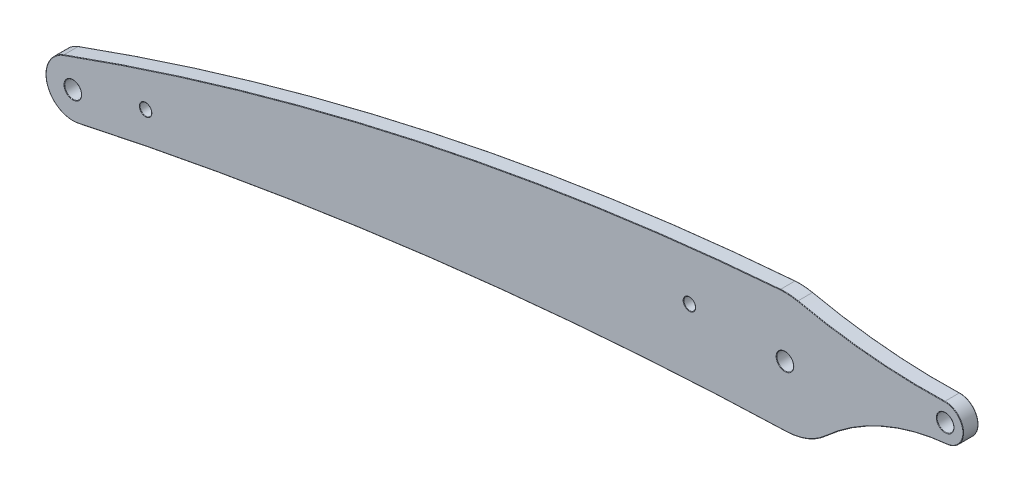
SolidWorks part; units mm, degrees
ref_plane "Front Plane" through (0, 0, 0) normal (0, 0, 1) x (1, 0, 0)
ref_plane "Top Plane" through (0, 0, 0) normal (0, 1, 0) x (1, 0, 0)
ref_plane "Right Plane" through (0, 0, 0) normal (1, 0, 0) x (0, 0, -1)
sketch "Sketch1" plane through (0, 0, 0) normal (0, 0, 1) x (1, 0, 0)
  line L0 (-273.7014, 238.8239) -> (16.1627, 287.9649) construction
  line L1 (-273.7014, 238.8239) -> (16.1627, 287.9649) construction
  circle A0 centre (-273.7014, 238.8239) radius 9 construction
  circle A1 centre (-37.0777, 278.939) radius 10 construction
  circle A2 centre (-37.0777, 278.939) radius 20 construction
  circle A3 centre (16.1627, 287.9649) radius 6 construction
  arc A4 (-276.7803, 247.2809) -> (-38.6275, 298.8789) centre (31.1135, -598.4149) cw
  arc A5 (-271.7936, 230.0285) -> (-36.4587, 258.9486) centre (3.7765, -1040.4286) cw
  arc A6 (-32.8087, 298.4781) -> (15.9797, 293.9621) centre (9.8804, 493.8691) ccw
  arc A7 (-23.6319, 264.1333) -> (16.7363, 281.9924) centre (23.4283, 212.313) cw
  arc A8 (-38.6275, 298.8789) -> (-32.8087, 298.4781) centre (-37.0777, 278.939) cw
  arc A9 (-23.6319, 264.1333) -> (-36.4587, 258.9486) centre (-37.0777, 278.939) cw
  arc A10 (15.9797, 293.9621) -> (16.7363, 281.9924) centre (16.1627, 287.9649) cw
  arc A11 (-276.7803, 247.2809) -> (-271.7936, 230.0285) centre (-273.7014, 238.8239) ccw
  arc A12 (-273.7014, 238.8239) -> (16.1627, 287.9649) centre (120.7432, -1208.3849) cw construction
  circle A13 centre (-273.7014, 238.8239) radius 2.8
  circle A14 centre (-249.5273, 245.1968) radius 1.95
  circle A15 centre (-68.8277, 279.5878) radius 1.95
  circle A16 centre (-37.0777, 278.939) radius 2.8
  circle A17 centre (16.1627, 287.9649) radius 2.8
  point P2 (-37.0777, 278.939)
  point P26 (-68.8277, 279.5878)
  point P27 (-249.5273, 245.1968)
  dimension "D1" = 18
  dimension "D2" = 40
  dimension "D3" = 20
  dimension "D4" = 12
  dimension "D5" = 1300
  dimension "D6" = 900
  dimension "D7" = 200
  dimension "D8" = 70
  dimension "D9" = 1500
  dimension "D12" = 5.6
  dimension "D13" = 3.9
  dimension "D14" = 5.6
  dimension "D10" = 31.75
  dimension "D11" = 25
extrude "Boss-Extrude1" add sketch "Sketch1" against normal blind 5
fillet "Fillet1" radius 0.15 26 edges at (-154.7868, 249.865, -5) (-29.5827, 260.3965, -5) (-4.8924, 276.3281, -5) (22.1507, 288.3434, -5) (-8.5533, 294.7204, -5) (-35.7034, 298.8918, -5) (-159.4582, 281.1773, -5) (-282.3474, 236.3248, -5) (-270.9014, 238.8239, -5) (-247.5773, 245.1968, -5) (-66.8777, 279.5878, -5) (-34.2777, 278.939, -5) (18.9627, 287.9649, -5) (-159.4582, 281.1773, 0) (-35.7034, 298.8918, 0) (-8.5533, 294.7204, 0) (22.1507, 288.3434, 0) (-4.8924, 276.3281, 0) (-29.5827, 260.3965, 0) (-154.7868, 249.865, 0) (-282.3474, 236.3248, 0) (-270.9014, 238.8239, 0) (-247.5773, 245.1968, 0) (-66.8777, 279.5878, 0) (-34.2777, 278.939, 0) (18.9627, 287.9649, 0)
